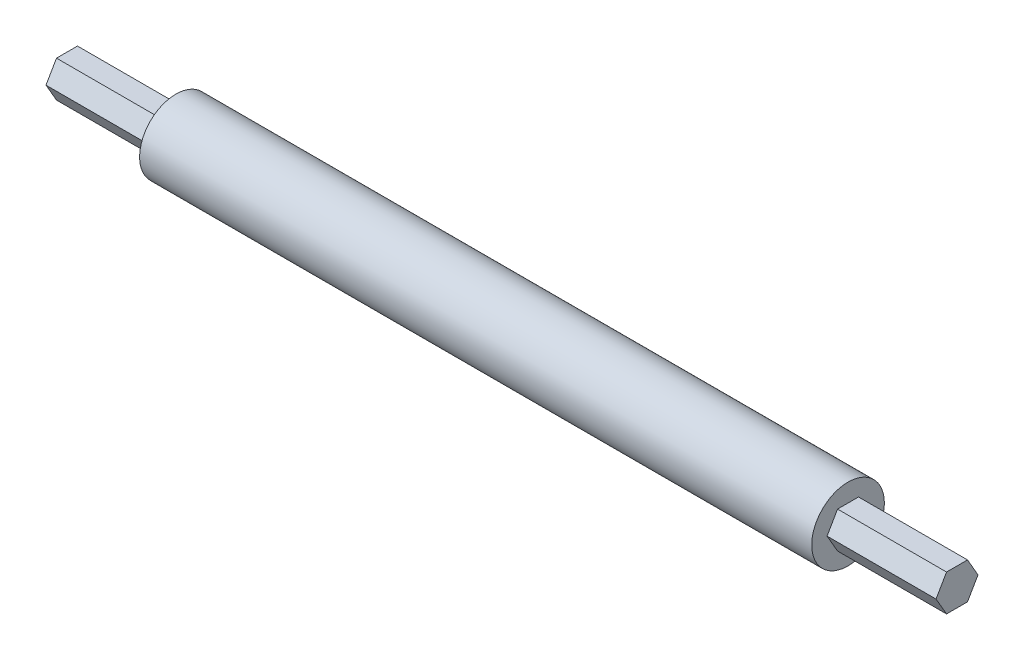
SolidWorks part; units mm, degrees
ref_plane "Front Plane" through (0, 0, 0) normal (0, 0, 1) x (1, 0, 0)
ref_plane "Top Plane" through (0, 0, 0) normal (0, 1, 0) x (1, 0, 0)
ref_plane "Right Plane" through (0, 0, 0) normal (1, 0, 0) x (0, 0, -1)
sketch "Sketch1" plane through (0, 0, 0) normal (1, 0, 0) x (0, 0, -1)
  line L1 (3.6662, 6.35) -> (-3.6662, 6.35)
  line L2 (-3.6662, 6.35) -> (-7.3323, 0)
  line L3 (-7.3323, 0) -> (-3.6662, -6.35)
  line L4 (-3.6662, -6.35) -> (3.6662, -6.35)
  line L5 (3.6662, -6.35) -> (7.3323, 0)
  line L6 (7.3323, 0) -> (3.6662, 6.35)
  circle A1 centre (0, 0) radius 6.35 construction
  dimension "D1" = 12.7
extrude "Boss-Extrude1" add sketch "Sketch1" along normal mid plane 311.15
sketch "Sketch2" plane through (0, 0, 0) normal (1, 0, 0) x (0, 0, -1)
  circle A0 centre (0, 0) radius 7.3323
sketch "Sketch3" plane through (0, 0, 0) normal (1, 0, 0) x (0, 0, -1)
  circle A0 centre (0, 0) radius 12.7
  dimension "D1" = 25.4
extrude "Boss-Extrude2" add sketch "Sketch3" along normal mid plane 234.95
